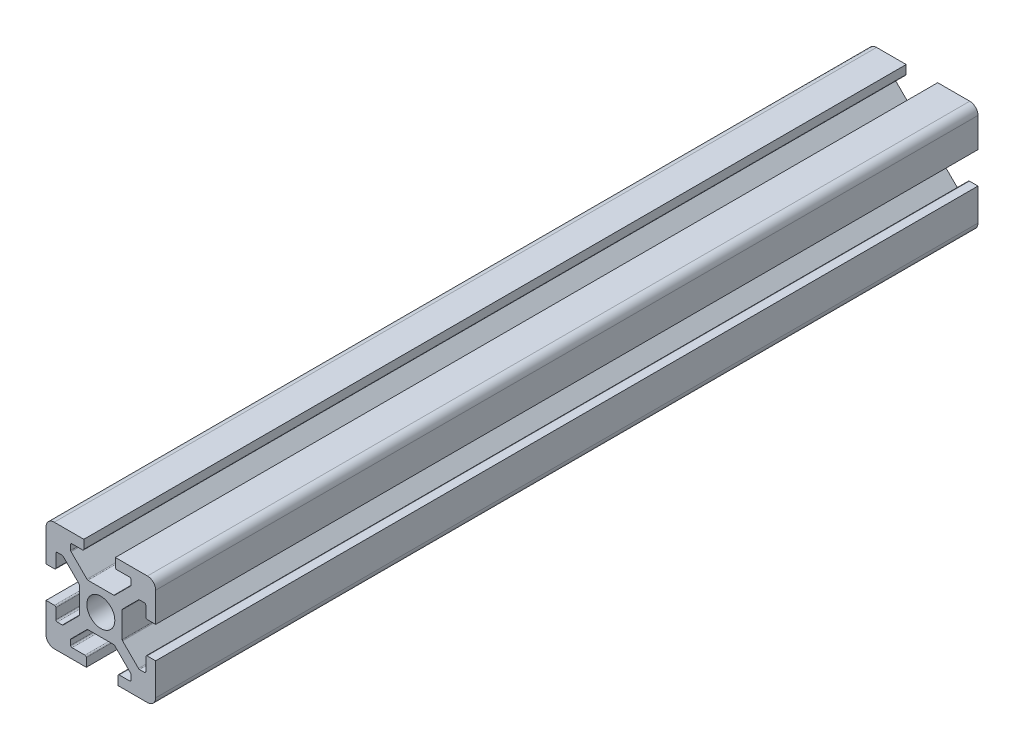
SolidWorks part; units mm, degrees
ref_plane "Front Plane" through (0, 0, 0) normal (0, 0, 1) x (1, 0, 0)
ref_plane "Top Plane" through (0, 0, 0) normal (0, 1, 0) x (1, 0, 0)
ref_plane "Right Plane" through (0, 0, 0) normal (1, 0, 0) x (0, 0, -1)
sketch "Sketch1" plane through (0, 0, 0) normal (0, 0, 1) x (1, 0, 0)
  line L1 (-8.5, -10) -> (-2.6476, -10)
  line L2 (-10, -8.5) -> (-10, -3.1)
  line L3 (-8.5, 10) -> (-3.1, 10)
  line L4 (10, -8.5) -> (10, -2.6476)
  line L5 (-1.8031, 1.8031) -> (1.8031, -1.8031) construction
  line L6 (-10, 10) -> (-3.9, 3.9) construction
  line L7 (2.3464, -3.9) -> (-2.3464, -3.9)
  line L8 (3.9, -2.3464) -> (3.9, 2.3464)
  line L9 (2.3464, 3.9) -> (-2.3464, 3.9)
  line L10 (-3.9, -2.3464) -> (-3.9, 2.3464)
  line L11 (1.8031, -1.8031) -> (-1.8031, 1.8031) construction
  line L12 (1.8031, 1.8031) -> (-1.8031, -1.8031) construction
  line L14 (-10, 2.6476) -> (-10, 8.5)
  line L15 (-10, 2.6476) -> (-8.45, 2.6476)
  line L17 (-10, -3.1) -> (-8.45, -3.1)
  line L18 (-3.9, 2.3464) -> (-3.9, -2.3464)
  line L19 (-8.2, 2.8976) -> (-8.2, 5.25)
  line L20 (-8.2, -3.35) -> (-8.2, -5.25)
  line L21 (-7.95, 5.5) -> (-7.0536, 5.5)
  line L22 (-6.8768, 5.4268) -> (-3.9732, 2.5232)
  line L23 (-6.8768, -5.4268) -> (-3.9732, -2.5232)
  line L24 (-7.95, -5.5) -> (-7.0536, -5.5)
  line L26 (-2.3464, 3.9) -> (2.3464, 3.9)
  line L27 (3.9, 3.9) -> (10, 10) construction
  line L28 (2.6476, 10) -> (2.6476, 8.45)
  line L29 (-3.1, 10) -> (-3.1, 8.45)
  line L30 (2.3464, 3.9) -> (-2.3464, 3.9)
  line L31 (2.8976, 8.2) -> (5.25, 8.2)
  line L32 (-3.35, 8.2) -> (-5.25, 8.2)
  line L33 (5.5, 7.95) -> (5.5, 7.0536)
  line L34 (5.4268, 6.8768) -> (2.5232, 3.9732)
  line L35 (-5.4268, 6.8768) -> (-2.5232, 3.9732)
  line L36 (-5.5, 7.95) -> (-5.5, 7.0536)
  line L37 (-1.8031, -1.8031) -> (1.8031, 1.8031) construction
  line L38 (3.9, 2.3464) -> (3.9, -2.3464)
  line L40 (10, -2.6476) -> (8.45, -2.6476)
  line L41 (10, 3.1) -> (8.45, 3.1)
  line L42 (3.9, -2.3464) -> (3.9, 2.3464)
  line L43 (8.2, -2.8976) -> (8.2, -5.25)
  line L44 (8.2, 3.35) -> (8.2, 5.25)
  line L45 (7.95, -5.5) -> (7.0536, -5.5)
  line L46 (6.8768, -5.4268) -> (3.9732, -2.5232)
  line L47 (6.8768, 5.4268) -> (3.9732, 2.5232)
  line L48 (7.95, 5.5) -> (7.0536, 5.5)
  line L50 (2.3464, -3.9) -> (-2.3464, -3.9)
  line L52 (-2.6476, -10) -> (-2.6476, -8.45)
  line L53 (3.1, -10) -> (3.1, -8.45)
  line L54 (-2.3464, -3.9) -> (2.3464, -3.9)
  line L55 (-2.8976, -8.2) -> (-5.25, -8.2)
  line L56 (3.35, -8.2) -> (5.25, -8.2)
  line L57 (-5.5, -7.95) -> (-5.5, -7.0536)
  line L58 (-5.4268, -6.8768) -> (-2.5232, -3.9732)
  line L59 (5.4268, -6.8768) -> (2.5232, -3.9732)
  line L60 (5.5, -7.95) -> (5.5, -7.0536)
  line L61 (2.6476, 10) -> (8.5, 10)
  line L62 (3.1, -10) -> (8.5, -10)
  line L63 (10, 3.1) -> (10, 8.5)
  line L65 (3.9, -3.9) -> (10, -10) construction
  circle A0 centre (0, 0) radius 2.55
  arc A1 (-8.2, -3.35) -> (-8.45, -3.1) centre (-8.45, -3.35) ccw
  arc A2 (-8.2, -5.25) -> (-7.95, -5.5) centre (-7.95, -5.25) ccw
  arc A3 (-6.8768, -5.4268) -> (-7.0536, -5.5) centre (-7.0536, -5.25) cw
  arc A4 (-3.9732, -2.5232) -> (-3.9, -2.3464) centre (-4.15, -2.3464) ccw
  arc A5 (-3.9, 2.3464) -> (-3.9732, 2.5232) centre (-4.15, 2.3464) ccw
  arc A6 (-7.0536, 5.5) -> (-6.8768, 5.4268) centre (-7.0536, 5.25) cw
  arc A7 (-8.2, 5.25) -> (-7.95, 5.5) centre (-7.95, 5.25) cw
  arc A8 (-8.2, 2.8976) -> (-8.45, 2.6476) centre (-8.45, 2.8976) cw
  arc A9 (-3.35, 8.2) -> (-3.1, 8.45) centre (-3.35, 8.45) ccw
  arc A10 (-5.25, 8.2) -> (-5.5, 7.95) centre (-5.25, 7.95) ccw
  arc A11 (-5.4268, 6.8768) -> (-5.5, 7.0536) centre (-5.25, 7.0536) cw
  arc A12 (-2.5232, 3.9732) -> (-2.3464, 3.9) centre (-2.3464, 4.15) ccw
  arc A13 (2.3464, 3.9) -> (2.5232, 3.9732) centre (2.3464, 4.15) ccw
  arc A14 (5.5, 7.0536) -> (5.4268, 6.8768) centre (5.25, 7.0536) cw
  arc A15 (5.25, 8.2) -> (5.5, 7.95) centre (5.25, 7.95) cw
  arc A16 (2.8976, 8.2) -> (2.6476, 8.45) centre (2.8976, 8.45) cw
  arc A17 (8.2, 3.35) -> (8.45, 3.1) centre (8.45, 3.35) ccw
  arc A18 (8.2, 5.25) -> (7.95, 5.5) centre (7.95, 5.25) ccw
  arc A19 (6.8768, 5.4268) -> (7.0536, 5.5) centre (7.0536, 5.25) cw
  arc A20 (3.9732, 2.5232) -> (3.9, 2.3464) centre (4.15, 2.3464) ccw
  arc A21 (3.9, -2.3464) -> (3.9732, -2.5232) centre (4.15, -2.3464) ccw
  arc A22 (7.0536, -5.5) -> (6.8768, -5.4268) centre (7.0536, -5.25) cw
  arc A23 (8.2, -5.25) -> (7.95, -5.5) centre (7.95, -5.25) cw
  arc A24 (8.2, -2.8976) -> (8.45, -2.6476) centre (8.45, -2.8976) cw
  arc A25 (3.35, -8.2) -> (3.1, -8.45) centre (3.35, -8.45) ccw
  arc A26 (5.25, -8.2) -> (5.5, -7.95) centre (5.25, -7.95) ccw
  arc A27 (5.4268, -6.8768) -> (5.5, -7.0536) centre (5.25, -7.0536) cw
  arc A28 (2.5232, -3.9732) -> (2.3464, -3.9) centre (2.3464, -4.15) ccw
  arc A29 (-2.3464, -3.9) -> (-2.5232, -3.9732) centre (-2.3464, -4.15) ccw
  arc A30 (-5.5, -7.0536) -> (-5.4268, -6.8768) centre (-5.25, -7.0536) cw
  arc A31 (-5.25, -8.2) -> (-5.5, -7.95) centre (-5.25, -7.95) cw
  arc A32 (-2.8976, -8.2) -> (-2.6476, -8.45) centre (-2.8976, -8.45) cw
  arc A33 (-10, -8.5) -> (-8.5, -10) centre (-8.5, -8.5) ccw
  arc A34 (8.5, -10) -> (10, -8.5) centre (8.5, -8.5) ccw
  arc A35 (10, 8.5) -> (8.5, 10) centre (8.5, 8.5) ccw
  arc A36 (-10, 8.5) -> (-8.5, 10) centre (-8.5, 8.5) cw
  point P15 (-10, -10)
  point P131 (0, 0)
  dimension "D1" = 20
  dimension "D4" = 5.1
  dimension "D5" = 0.25
  dimension "D6" = 1.5
  dimension "D2" = 20
  dimension "D3" = 4
extrude "Boss-Extrude1" add sketch "Sketch1" along normal blind 150 contours A36 L14 L15 A8 L19 A7 L21 A6 L22 A5 L10 A4 L23 A3 L24 A2 L20 A1 L17 L2 A33 L1 L52 A32 L55 A31 L57 A30 L58 A29 L7 A28 L59 A27 L60 A26 L56 A25 L53 L62 A34 L4 L40 A24 L43 A23 L45 A22 L46 A21 L8
